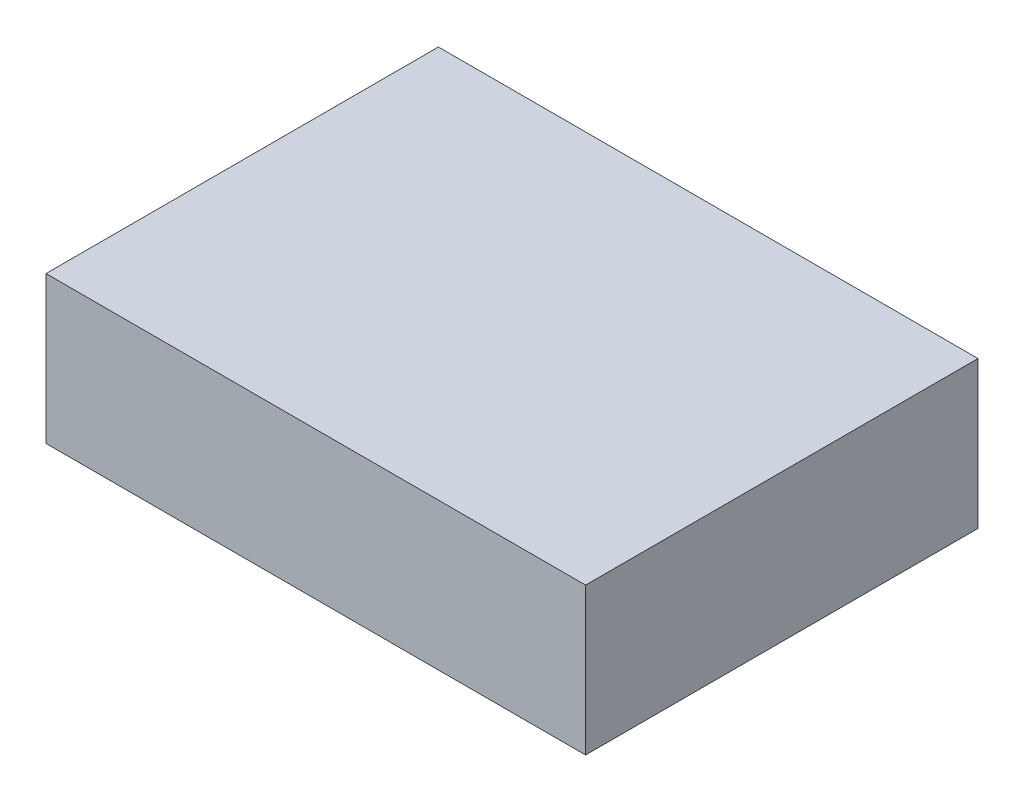
SolidWorks part; units mm, degrees
material "Plain Carbon Steel"
ref_plane "Front Plane" through (0, 0, 0) normal (0, 0, 1) x (1, 0, 0)
ref_plane "Top Plane" through (0, 0, 0) normal (0, 1, 0) x (1, 0, 0)
ref_plane "Right Plane" through (0, 0, 0) normal (1, 0, 0) x (0, 0, -1)
sketch "Sketch1" plane through (0, 0, 0) normal (0, 1, 0) x (1, 0, 0)
  line L1 (-36.3233, 16.1876) -> (33.5267, 16.1876)
  line L2 (-36.3233, 16.1876) -> (-36.3233, -34.6124)
  line L3 (-36.3233, -34.6124) -> (33.5267, -34.6124)
  line L4 (33.5267, 16.1876) -> (33.5267, -34.6124)
  dimension "D1" = 50.8
  dimension "D2" = 69.85
extrude "Boss-Extrude1" add sketch "Sketch1" along normal blind 19.05
